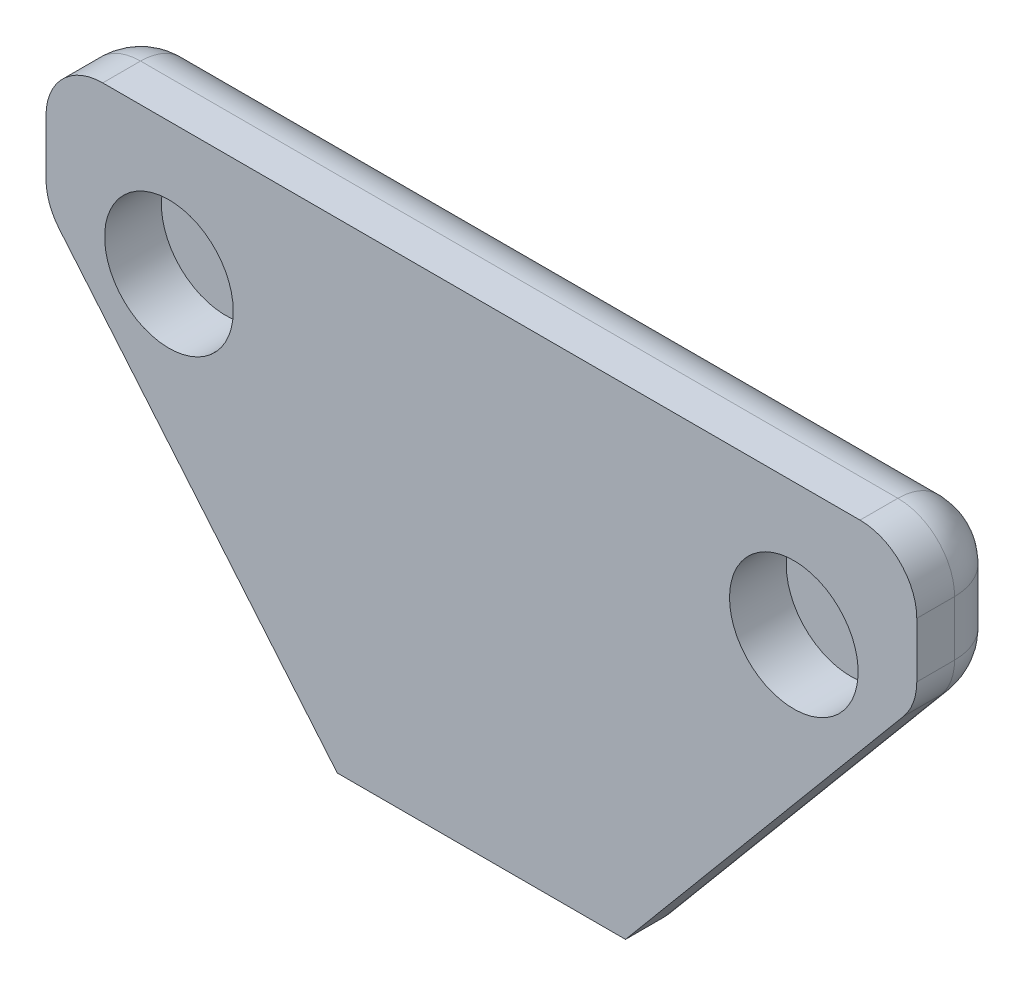
SolidWorks part; units mm, degrees
ref_plane "Front Plane" through (0, 0, 0) normal (0, 0, 1) x (1, 0, 0)
ref_plane "Top Plane" through (0, 0, 0) normal (0, 1, 0) x (1, 0, 0)
ref_plane "Right Plane" through (0, 0, 0) normal (1, 0, 0) x (0, 0, -1)
sketch "Sketch1" plane through (0, 0, 0) normal (0, 0, 1) x (1, 0, 0)
  line L0 (-6.0642, 12.7) -> (-6.0642, 9.2)
  line L1 (-6.0642, 9.2) -> (1.6358, 0)
  line L2 (5.4458, 0) -> (1.6358, 0)
  line L4 (5.4458, 0) -> (5.4458, 12.7)
  line L6 (5.4458, 12.7) -> (-6.0642, 12.7)
  line L7 (-2.8142, 12.7) -> (-2.8142, 5.3169) construction
  line L8 (-6.0642, 9.2) -> (5.4458, 9.2) construction
  dimension "D1" = 3.5
  dimension "D2" = 3.25
  dimension "D3" = 12.7
  dimension "D4" = 3.81
  dimension "D5" = 11.51
extrude "Boss-Extrude1" add sketch "Sketch1" along normal blind 2.5
sketch "Sketch2" plane through (0, 0, 2.5) normal (0, 0, 1) x (1, 0, 0)
  line L0 (-6.0642, 9.2) -> (5.4458, 9.2) construction
  line L1 (-6.0642, 12.7) -> (-6.0642, 9.2) construction
  line L2 (5.4458, 0) -> (5.4458, 12.7) construction
  line L3 (-2.8142, 12.7) -> (-2.8142, 0) construction
  line L4 (5.4458, 12.7) -> (-6.0642, 12.7) construction
  line L5 (1.6358, 0) -> (5.4458, 0) construction
  circle A0 centre (-2.8142, 9.2) radius 1.7
  dimension "D1" = 3.5
  dimension "D2" = 3.25
extrude "Cut-Extrude1" cut sketch "Sketch2" against normal blind 1.5
fillet "Fillet1" radius 1.5 6 edges at (-6.0642, 12.7, 1.25) (-6.0642, 9.2, 1.25) (3.5408, 0, 0) (-2.2142, 4.6, 0) (-6.0642, 10.95, 0) (-0.3092, 12.7, 0)
mirror "Mirror2" about plane through (5.4458, 0, 2.5) normal (-1, 0, 0) of bodies 103
